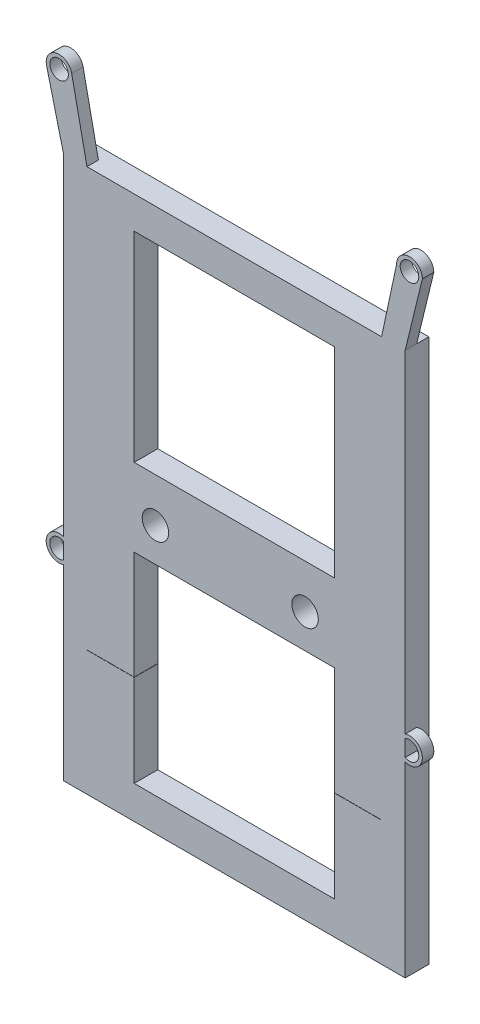
SolidWorks part; units mm, degrees
ref_plane "前基準面" through (0, 0, 0) normal (0, 0, 1) x (1, 0, 0)
ref_plane "上基準面" through (0, 0, 0) normal (0, 1, 0) x (1, 0, 0)
ref_plane "右基準面" through (0, 0, 0) normal (1, 0, 0) x (0, 0, -1)
sketch "草圖1" plane through (0, 0, 0) normal (0, 0, 1) x (1, 0, 0)
  line L0 (1.2262, 28.739) -> (1.2262, 10.1035) construction
  line L2 (21.9262, 28.739) -> (21.9262, -28.6267)
  line L3 (21.9262, -28.6267) -> (-19.2738, -28.6267)
  line L4 (-19.2738, 28.739) -> (-19.2738, -28.6267)
  line L7 (-19.2738, 28.739) -> (-19.2738, 29.889)
  line L8 (-19.2738, 29.889) -> (21.9262, 29.889)
  line L9 (21.9262, 28.739) -> (21.9262, 29.889)
  line L10 (-19.2738, 29.889) -> (-22.5738, 29.889)
  line L11 (-19.2738, 29.889) -> (-19.2738, -28.6267)
  line L12 (-19.2738, -28.6267) -> (-22.5738, -28.6267)
  line L13 (-22.5738, 29.889) -> (-22.5738, -28.6267)
  circle A0 centre (11.2262, -8.761) radius 1.85
  circle A1 centre (-9.7, -8.761) radius 1.85
  point P14 (0, 0)
  point P15 (0, 0)
  point P16 (0, 0)
  point P17 (0, 0)
  point P18 (0, 0)
  point P19 (0, 0)
  dimension "D1" = 41.2
  dimension "D6" = 1.15
extrude "填料-伸長1" add sketch "草圖1" against normal blind 3.3 contours L2 L3 L4 L7 L8 L9 | A0 | A1
sketch "草圖2" plane through (0, 0, 0) normal (0, 0, 1) x (1, 0, 0)
  line L1 (21.9262, 29.889) -> (25.2262, 29.889)
  line L2 (21.9262, 29.889) -> (21.9262, -28.6555)
  line L3 (21.9262, -28.6555) -> (25.2262, -28.6555)
  line L4 (25.2262, 29.889) -> (25.2262, -28.6555)
  line L5 (-19.2738, 29.889) -> (-22.5738, 29.889)
  line L6 (-19.2738, 29.889) -> (-19.2738, -28.6555)
  line L7 (-19.2738, -28.6555) -> (-22.5738, -28.6555)
  line L8 (-22.5738, 29.889) -> (-22.5738, -28.6555)
  dimension "D1" = 3.3
  dimension "D2" = 3.3
extrude "填料-伸長2" add sketch "草圖2" against normal blind 3.3 separate body contours L4 L1 L2 L3 | L6 L5 L8 L7
sketch "草圖3" plane through (0, 0, 0) normal (0, 0, 1) x (1, 0, 0)
  line L0 (-22.5738, 29.889) -> (-22.5738, -28.6555) construction
  line L5 (-22.5738, -28.6555) -> (-22.5738, -46.1155)
  line L6 (25.2262, 29.889) -> (25.2262, -28.6555) construction
  line L7 (-22.5738, -28.6555) -> (25.2262, -28.6555)
  line L8 (-22.5738, -28.6555) -> (-22.5738, -46.1155)
  line L9 (-22.5738, -46.1155) -> (25.2262, -46.1155)
  line L10 (25.2262, -28.6555) -> (25.2262, -46.1155)
extrude "填料-伸長3" add sketch "草圖3" against normal blind 3.3 contours L8 L7 L10 L9
sketch "草圖4" plane through (0, 0, 0) normal (0, 0, 1) x (1, 0, 0)
  line L0 (-22.5738, -8.1133) -> (34.2643, -8.1133) construction
  line L1 (1.3262, 29.889) -> (1.3262, 15.2872) construction
  line L3 (-12.6738, -41.495) -> (15.3262, -41.495)
  line L4 (-12.6738, 25.3794) -> (15.3262, 25.3794)
  line L5 (-12.6738, 25.3794) -> (-12.6738, -2.6206)
  line L6 (-12.6738, -2.6206) -> (15.3262, -2.6206)
  line L7 (15.3262, 25.3794) -> (15.3262, -2.6206)
  line L8 (-12.6738, -41.495) -> (-12.6738, -13.495)
  line L9 (-12.6738, -13.495) -> (15.3262, -13.495)
  line L10 (15.3262, -41.495) -> (15.3262, -13.495)
  point P4 (1.3262, 25.3794)
  dimension "D1" = 28
  dimension "D2" = 28
  dimension "D3" = 28
extrude "除料-伸長2" cut sketch "草圖4" against normal blind 3.3
sketch "草圖5" plane through (0, 0, 0) normal (0, 0, 1) x (1, 0, 0)
  line L0 (24.0262, 39.7403) -> (21.9262, 29.889)
  line L5 (1.3262, 29.889) -> (1.3262, 21.0171) construction
  line L6 (27.6262, 39.7403) -> (25.2262, 29.889)
  line L7 (-22.5738, 29.889) -> (-24.9204, 39.305)
  line L8 (-19.2738, 29.889) -> (-21.412, 40.1089)
  line L9 (21.9262, 29.889) -> (25.2262, 29.889)
  line L10 (-22.5738, 29.889) -> (-19.2738, 29.889)
  circle A0 centre (-23.1738, 39.7403) radius 1.3
  circle A1 centre (25.8262, 39.7403) radius 1.3
  circle A2 centre (-23.1738, -18.2597) radius 1.3
  circle A3 centre (25.8262, -18.2597) radius 1.3
  circle A4 centre (-23.1738, -18.2597) radius 1.8
  circle A5 centre (25.8262, -18.2597) radius 1.8
  circle A6 centre (-23.1738, 39.7403) radius 1.8
  circle A7 centre (25.8262, 39.7403) radius 1.8
  dimension "D1" = 49
  dimension "D2" = 58
extrude "填料-伸長4" add sketch "草圖5" against normal blind 1.6 contours A6 A0 | A6 L7 L10 L8 | L6 A7 A1 | A7 L0 L9 L6 | A4 A2 | A5 A3
sketch "草圖6" plane through (0, 0, 0) normal (0, 0, 1) x (1, 0, 0)
  line L0 (-24.9204, 39.305) -> (-22.5738, 29.889)
  line L1 (-22.5738, 29.889) -> (-19.2738, 29.889)
  line L2 (-19.2738, 29.889) -> (-21.3777, 39.8584)
  line L3 (21.9262, 29.889) -> (25.2262, 29.889)
  line L4 (25.2262, 29.889) -> (27.6262, 39.7403)
  line L5 (21.9262, 29.889) -> (24.0643, 40.1089)
  circle A0 centre (-23.1738, -18.2597) radius 1.8
  circle A1 centre (-23.1738, -18.2597) radius 1.3
  circle A2 centre (25.8262, -18.2597) radius 1.8
  circle A3 centre (25.8262, -18.2597) radius 1.3
  circle A4 centre (25.8262, 39.7403) radius 1.8
  circle A5 centre (25.8262, 39.7403) radius 1.3
  circle A6 centre (-23.1738, 39.7403) radius 1.3
  circle A7 centre (-23.1738, 39.7403) radius 1.8
ref_plane "平面1" through (-22.5738, 29.889, -3.3) normal (0, -1, 0) x (-1, 0, 0)
